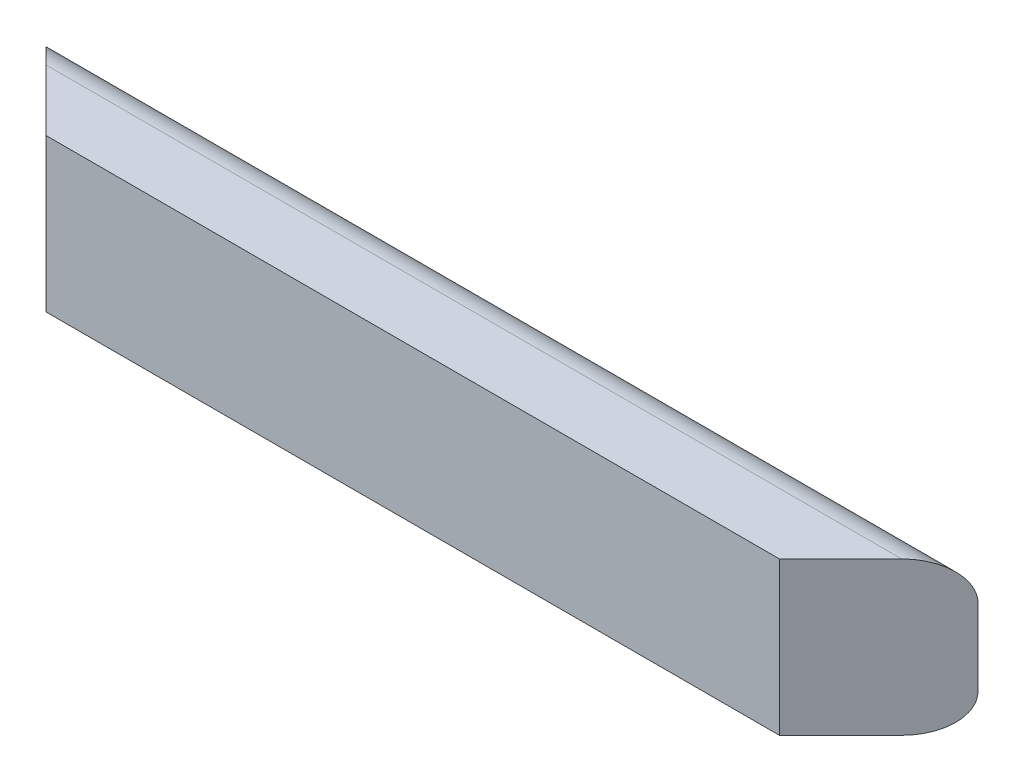
SolidWorks part; units mm, degrees
ref_plane "Front" through (0, 0, 0) normal (0, 0, 1) x (1, 0, 0)
ref_plane "Top" through (0, 0, 0) normal (0, 1, 0) x (1, 0, 0)
ref_plane "Right" through (0, 0, 0) normal (1, 0, 0) x (0, 0, -1)
sketch "Sketch1" plane through (0, 0, 0) normal (1, 0, 0) x (0, 0, -1)
  line L0 (0, 0) -> (0, 127) construction
  line L1 (0, 0) -> (31.75, 0)
  line L2 (31.75, 127) -> (0, 127)
  line L3 (63.5, 95.25) -> (63.5, 31.75)
  line L4 (0, 0) -> (-19.05, 0)
  line L5 (-19.05, 0) -> (-19.05, 127)
  line L6 (-19.05, 127) -> (0, 127)
  arc A0 (31.75, 0) -> (63.5, 31.75) centre (31.75, 31.75) ccw
  arc A1 (63.5, 95.25) -> (31.75, 127) centre (31.75, 95.25) ccw
  dimension "D2" = 63.5
  dimension "D1" = 19.05
extrude "Boss-Extrude1" add sketch "Sketch1" along normal blind 774.7
ref_plane "Mid_Plane" through (387.35, 0, 0) normal (1, 0, 0) x (0, 0, -1)
ref_plane "Plane1" through (355.6, 0, 355.6) normal (0.7071, 0, 0.7071) x (0, 1, 0)
sketch "Sketch2" plane through (355.6, 0, 355.6) normal (0.7071, 0, 0.7071) x (0, 1, 0)
  line L0 (31.75, -592.6969) -> (95.25, -592.6969) construction
  line L1 (205.1964, -202.4681) -> (-139.2061, -202.4681)
  line L2 (205.1964, -202.4681) -> (205.1964, -982.9257)
  line L3 (205.1964, -982.9257) -> (-139.2061, -982.9257)
  line L4 (-139.2061, -202.4681) -> (-139.2061, -982.9257)
  line L5 (205.1964, -202.4681) -> (-139.2061, -982.9257) construction
  line L6 (205.1964, -982.9257) -> (-139.2061, -202.4681) construction
  point P4 (32.9952, -592.6969)
  point P5 (0, 0)
  point P8 (0, 0)
extrude "Cut-Extrude1" cut sketch "Sketch2" along normal through all
mirror "Mirror1" about plane through (387.35, 0, 0) normal (1, 0, 0) of "Cut-Extrude1"
